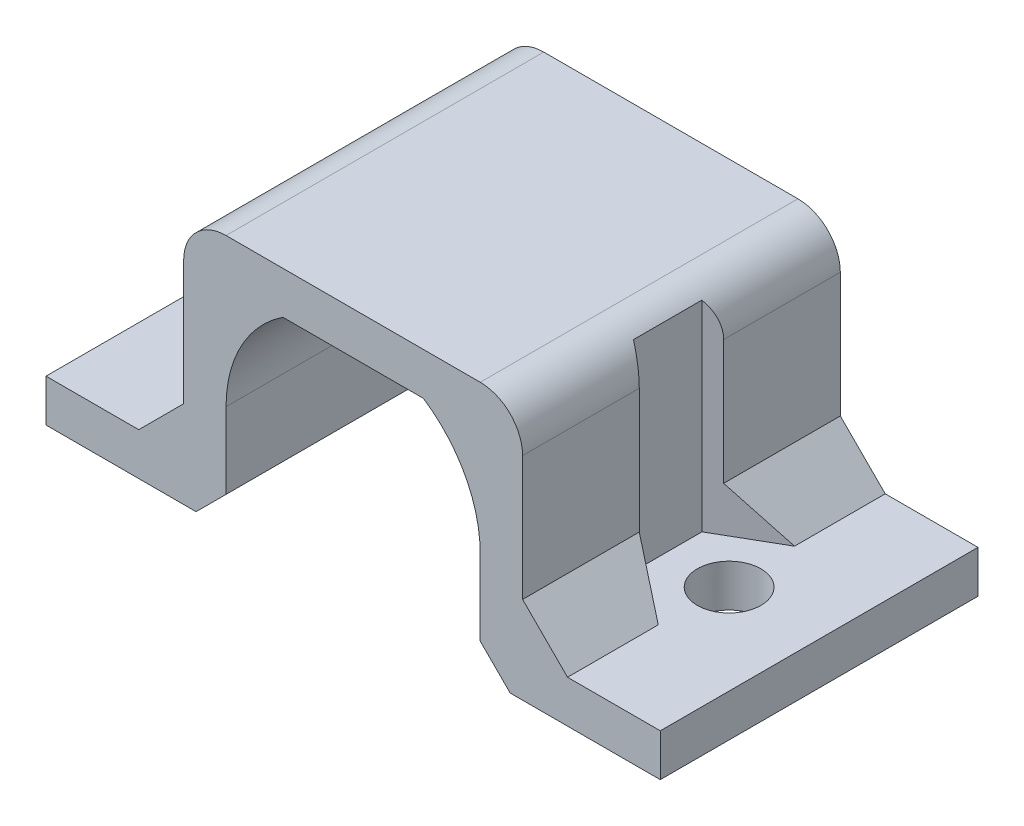
SolidWorks part; units mm, degrees
material "ABS"
ref_plane "Alzado" through (0, 0, 0) normal (0, 0, 1) x (1, 0, 0)
ref_plane "Planta" through (0, 0, 0) normal (0, 1, 0) x (1, 0, 0)
ref_plane "Vista lateral" through (0, 0, 0) normal (1, 0, 0) x (0, 0, -1)
sketch "Croquis1" plane through (0, 0, 0) normal (0, 0, 1) x (1, 0, 0)
  line L0 (14.5, 0) -> (7.4142, 0)
  line L1 (7.4142, 0) -> (6, 1.4142)
  line L2 (6, 1.4142) -> (6, 5)
  line L3 (3.3166, 10) -> (-3.3166, 10)
  line L4 (-8, 12) -> (8, 12)
  line L5 (8, 12) -> (8, 4.1213)
  line L6 (8, 4.1213) -> (10.1213, 2)
  line L7 (10.1213, 2) -> (14.5, 2)
  line L8 (14.5, 2) -> (14.5, 0)
  line L10 (0, 0) -> (0, 50000) construction
  line L12 (-14.5, 2) -> (-14.5, 0)
  line L13 (-10.1213, 2) -> (-14.5, 2)
  line L14 (-8, 4.1213) -> (-10.1213, 2)
  line L15 (-8, 12) -> (-8, 4.1213)
  line L16 (-6, 1.4142) -> (-6, 5)
  line L17 (-7.4142, 0) -> (-6, 1.4142)
  line L18 (-14.5, 0) -> (-7.4142, 0)
  arc A0 (6, 5) -> (3.3166, 10) centre (0, 5) ccw
  arc A3 (-6, 5) -> (-3.3166, 10) centre (0, 5) cw
  point P7 (0, 10)
  point P29 (0, 12)
  dimension "D10" = 3
  dimension "D1" = 12
  dimension "D2" = 10
  dimension "D3" = 2
  dimension "D4" = 2
  dimension "D5" = 45
  dimension "D6" = 2
  dimension "D7" = 2
  dimension "D8" = 8.5
  dimension "D9" = 5
extrude "Saliente-Extruir1" add sketch "Croquis1" along normal mid plane 15
fillet "Redondeo1" radius 2 2 edges at (-8, 12, 0) (8, 12, 0)
sketch "Croquis3" plane through (0, 12, 0) normal (0, 1, 0) x (1, 0, 0)
  line L0 (0, 0) -> (0, 9.6966) construction
  line L1 (-10.15, -3.2332) -> (-7.35, -1.6166)
  line L2 (-7.35, -1.6166) -> (-7.35, 1.6166)
  line L3 (-7.35, 1.6166) -> (-10.15, 3.2332)
  line L4 (-10.15, 3.2332) -> (-12.95, 1.6166)
  line L5 (-12.95, 1.6166) -> (-12.95, -1.6166)
  line L6 (-12.95, -1.6166) -> (-10.15, -3.2332)
  line L7 (12.95, -1.6166) -> (10.15, -3.2332)
  line L8 (12.95, 1.6166) -> (12.95, -1.6166)
  line L9 (10.15, 3.2332) -> (12.95, 1.6166)
  line L10 (7.35, 1.6166) -> (10.15, 3.2332)
  line L11 (7.35, -1.6166) -> (7.35, 1.6166)
  line L12 (10.15, -3.2332) -> (7.35, -1.6166)
  line L13 (-14.5, -7.5) -> (-14.5, 7.5) construction
  circle A0 centre (-10.15, 0) radius 2.8 construction
  circle A1 centre (10.15, 0) radius 2.8 construction
  dimension "D1" = 5.6
  dimension "D2" = 1.55
extrude "Cortar-Extruir2" cut sketch "Croquis3" against normal up to surface (10 mm away) up to face at (-12.3107, 2, 0)
sketch "Croquis4" plane through (0, 0, 0) normal (0, -1, 0) x (1, 0, 0)
  line L0 (0, 0) -> (0, 8.3958) construction
  line L1 (-14.5, 7.5) -> (-14.5, -7.5) construction
  circle A0 centre (-10.25, 0) radius 1.5
  circle A1 centre (10.25, 0) radius 1.5
  dimension "D1" = 3
  dimension "D2" = 4.25
extrude "Cortar-Extruir3" cut sketch "Croquis4" against normal blind 11
